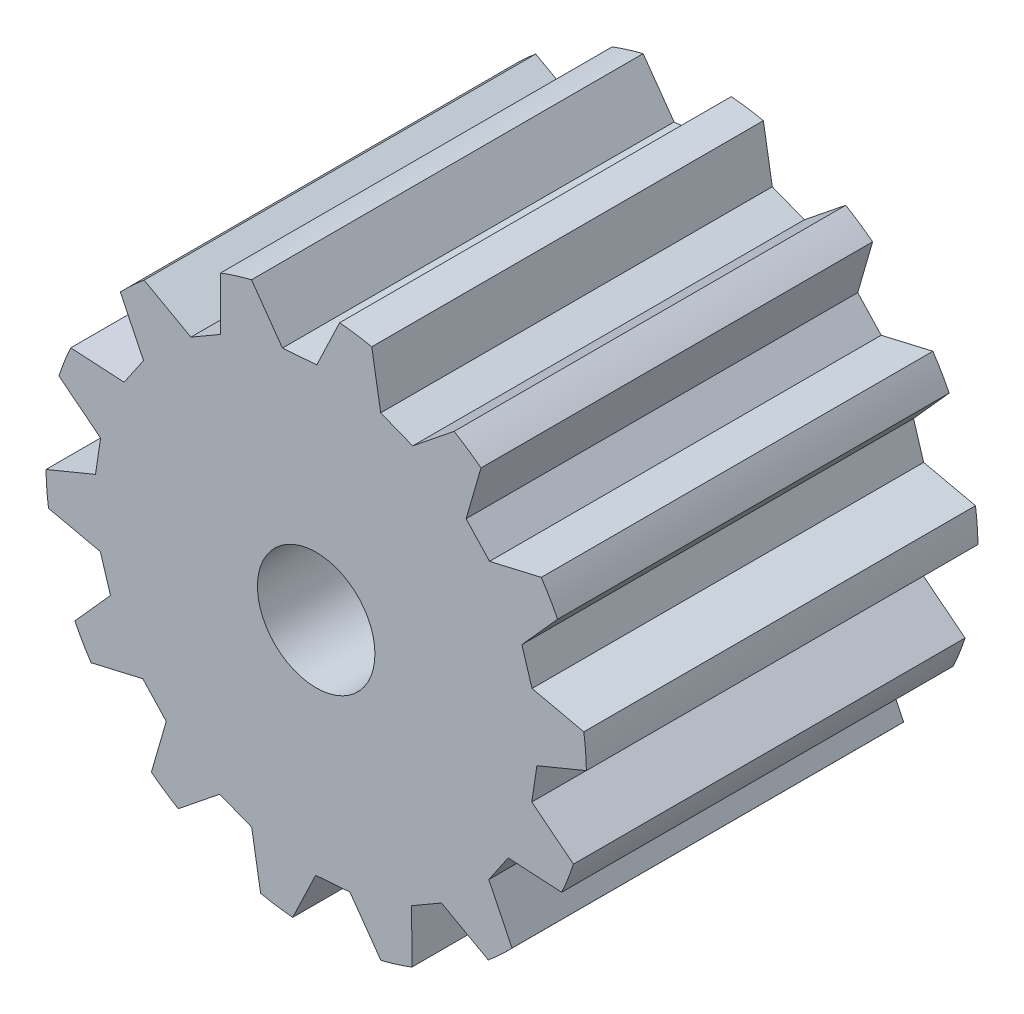
SolidWorks part; units mm, degrees
ref_plane "Front Plane" through (0, 0, 0) normal (0, 0, 1) x (1, 0, 0)
ref_plane "Top Plane" through (0, 0, 0) normal (0, 1, 0) x (1, 0, 0)
ref_plane "Right Plane" through (0, 0, 0) normal (1, 0, 0) x (0, 0, -1)
sketch "Sketch1" plane through (0, 0, 0) normal (0, 0, 1) x (1, 0, 0)
  line L0 (0, 0) -> (-1.6677, 5.3983) construction
  line L1 (-1.6677, 5.3983) -> (-2.0367, 6.5926) construction
  line L2 (-2.4381, 5.0969) -> (-2.4434, 6.4529)
  line L3 (-1.6512, 6.6995) -> (-0.8616, 5.5839)
  line L4 (0.0148, 5.65) -> (0.5984, 6.874)
  line L5 (1.4191, 6.7525) -> (1.6465, 5.4048)
  line L6 (2.4648, 5.084) -> (3.5217, 5.9336)
  line L7 (4.2084, 5.4681) -> (3.8285, 4.1551)
  line L8 (4.4266, 3.5111) -> (5.7474, 3.818)
  line L9 (6.1641, 3.1006) -> (5.2522, 2.0825)
  line L10 (5.5116, 1.2428) -> (6.8348, 0.9462)
  line L11 (6.899, 0.1191) -> (5.6356, -0.4025)
  line L12 (5.505, -1.2717) -> (6.5685, -2.113)
  line L13 (6.2674, -2.8861) -> (4.9029, -2.8079)
  line L14 (4.4081, -3.5343) -> (5.0012, -4.7537)
  line L15 (4.3945, -5.3196) -> (3.199, -4.6571)
  line L16 (2.4381, -5.0969) -> (2.4434, -6.4529)
  line L17 (1.6512, -6.6995) -> (0.8616, -5.5839)
  line L18 (-0.0148, -5.65) -> (-0.5984, -6.874)
  line L19 (-1.4191, -6.7525) -> (-1.6465, -5.4048)
  line L20 (-2.4648, -5.084) -> (-3.5217, -5.9336)
  line L21 (-4.2084, -5.4681) -> (-3.8285, -4.1551)
  line L22 (-4.4266, -3.5111) -> (-5.7474, -3.818)
  line L23 (-6.1641, -3.1006) -> (-5.2522, -2.0825)
  line L24 (-5.5116, -1.2428) -> (-6.8348, -0.9462)
  line L25 (-6.899, -0.1191) -> (-5.6356, 0.4025)
  line L26 (-5.505, 1.2717) -> (-6.5685, 2.113)
  line L27 (-6.2674, 2.8861) -> (-4.9029, 2.8079)
  line L28 (-4.4081, 3.5343) -> (-5.0012, 4.7537)
  line L29 (-4.3945, 5.3196) -> (-3.199, 4.6571)
  line L30 (-5.6356, 0.4025) -> (-5.505, 1.2717)
  line L31 (-4.9029, 2.8079) -> (-4.4081, 3.5343)
  line L32 (-3.199, 4.6571) -> (-2.4381, 5.0969)
  line L33 (-0.8616, 5.5839) -> (0.0148, 5.65)
  line L34 (1.6465, 5.4048) -> (2.4648, 5.084)
  line L35 (3.8285, 4.1551) -> (4.4266, 3.5111)
  line L36 (5.2522, 2.0825) -> (5.5116, 1.2428)
  line L37 (5.6356, -0.4025) -> (5.505, -1.2717)
  line L38 (4.9029, -2.8079) -> (4.4081, -3.5343)
  line L39 (3.199, -4.6571) -> (2.4381, -5.0969)
  line L40 (0.8616, -5.5839) -> (-0.0148, -5.65)
  line L41 (-1.6465, -5.4048) -> (-2.4648, -5.084)
  line L42 (-3.8285, -4.1551) -> (-4.4266, -3.5111)
  line L43 (-5.2522, -2.0825) -> (-5.5116, -1.2428)
  circle A0 centre (0, 0) radius 6.9 construction
  circle A1 centre (0, 0) radius 5.65 construction
  arc A2 (-0.8616, 5.5839) -> (-2.4381, 5.0969) centre (0, 0) ccw construction
  arc A3 (-1.6512, 6.6995) -> (-2.4434, 6.4529) centre (0, 0) ccw
  arc A4 (1.4191, 6.7525) -> (0.5984, 6.874) centre (0, 0) ccw
  arc A5 (4.2084, 5.4681) -> (3.5217, 5.9336) centre (0, 0) ccw
  arc A6 (6.1641, 3.1006) -> (5.7474, 3.818) centre (0, 0) ccw
  arc A7 (6.899, 0.1191) -> (6.8348, 0.9462) centre (0, 0) ccw
  arc A8 (6.2674, -2.8861) -> (6.5685, -2.113) centre (0, 0) ccw
  arc A9 (4.3945, -5.3196) -> (5.0012, -4.7537) centre (0, 0) ccw
  arc A10 (1.6512, -6.6995) -> (2.4434, -6.4529) centre (0, 0) ccw
  arc A11 (-1.4191, -6.7525) -> (-0.5984, -6.874) centre (0, 0) ccw
  arc A12 (-4.2084, -5.4681) -> (-3.5217, -5.9336) centre (0, 0) ccw
  arc A13 (-6.1641, -3.1006) -> (-5.7474, -3.818) centre (0, 0) ccw
  arc A14 (-6.899, -0.1191) -> (-6.8348, -0.9462) centre (0, 0) ccw
  arc A15 (-6.2674, 2.8861) -> (-6.5685, 2.113) centre (0, 0) ccw
  arc A16 (-4.3945, 5.3196) -> (-5.0012, 4.7537) centre (0, 0) ccw
  circle A31 centre (0, 0) radius 1.5
  point P65 (0, 0)
  point P93 (0, 0)
  point P94 (0, 0)
  dimension "D1" = 13.8
  dimension "D2" = 11.3
  dimension "D3" = 1.65
  dimension "D4" = 0.4
  dimension "D6" = 14
  dimension "D9" = 3
  dimension "D5" = 0.43
extrude "Boss-Extrude1" add sketch "Sketch1" along normal blind 10
